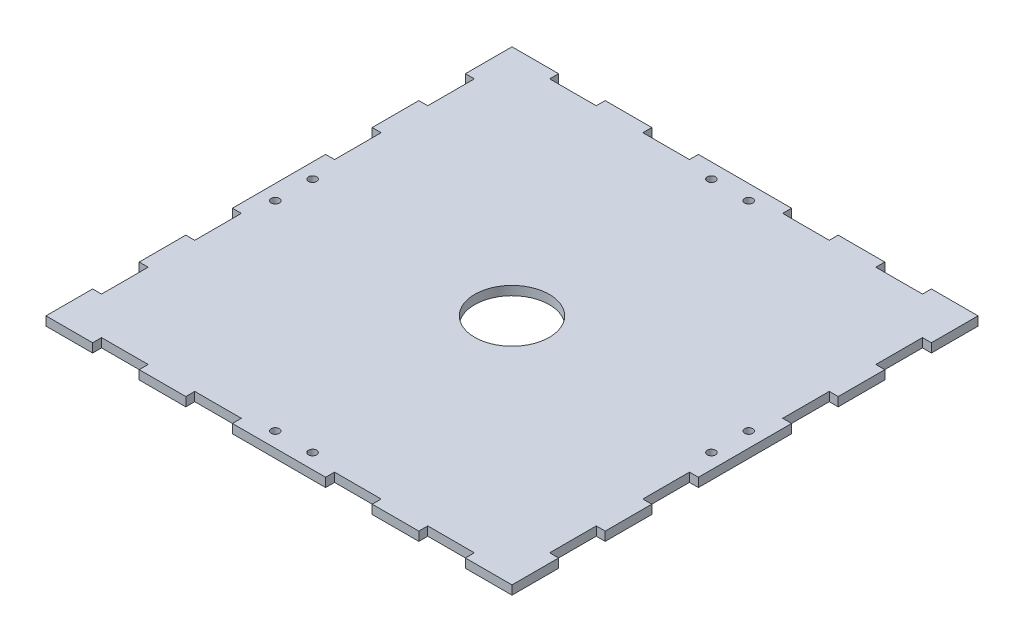
SolidWorks part; units mm, degrees
material "Acrylic (Medium-high impact)"
ref_plane "Front Plane" through (0, 0, 0) normal (0, 0, 1) x (1, 0, 0)
ref_plane "Top Plane" through (0, 0, 0) normal (0, 1, 0) x (1, 0, 0)
ref_plane "Right Plane" through (0, 0, 0) normal (1, 0, 0) x (0, 0, -1)
sketch "Sketch1" plane through (0, 0, 0) normal (0, 1, 0) x (1, 0, 0)
  line L0 (0, 79.375) -> (158.75, 79.375) construction
  line L1 (0, 0) -> (15.875, 0)
  line L2 (0, 0) -> (0, 15.875)
  line L3 (31.75, 158.75) -> (47.625, 158.75)
  line L4 (158.75, 0) -> (158.75, 15.875)
  line L5 (79.375, 158.75) -> (79.375, 0) construction
  line L6 (0, 0) -> (158.75, 158.75) construction
  line L7 (0, 158.75) -> (15.875, 158.75)
  line L8 (15.875, 158.75) -> (15.875, 155.702)
  line L9 (47.625, 158.75) -> (47.625, 155.702)
  line L10 (47.625, 155.702) -> (63.5, 155.702)
  line L11 (63.5, 155.702) -> (63.5, 158.75)
  line L12 (63.5, 158.75) -> (95.25, 158.75)
  line L13 (15.875, 155.702) -> (31.75, 155.702)
  line L14 (31.75, 155.702) -> (31.75, 158.75)
  line L15 (127, 155.702) -> (127, 158.75)
  line L16 (142.875, 155.702) -> (127, 155.702)
  line L17 (95.25, 155.702) -> (95.25, 158.75)
  line L18 (111.125, 155.702) -> (95.25, 155.702)
  line L19 (111.125, 158.75) -> (111.125, 155.702)
  line L20 (142.875, 158.75) -> (142.875, 155.702)
  line L21 (111.125, 158.75) -> (127, 158.75)
  line L22 (142.875, 158.75) -> (158.75, 158.75)
  line L23 (31.75, 3.048) -> (31.75, 0)
  line L24 (15.875, 3.048) -> (31.75, 3.048)
  line L25 (63.5, 3.048) -> (63.5, 0)
  line L26 (47.625, 3.048) -> (63.5, 3.048)
  line L27 (47.625, 0) -> (47.625, 3.048)
  line L28 (15.875, 0) -> (15.875, 3.048)
  line L29 (142.875, 0) -> (142.875, 3.048)
  line L30 (111.125, 0) -> (111.125, 3.048)
  line L31 (111.125, 3.048) -> (95.25, 3.048)
  line L32 (95.25, 3.048) -> (95.25, 0)
  line L33 (142.875, 3.048) -> (127, 3.048)
  line L34 (127, 3.048) -> (127, 0)
  line L35 (63.5, 0) -> (95.25, 0)
  line L36 (31.75, 0) -> (47.625, 0)
  line L37 (111.125, 0) -> (127, 0)
  line L38 (142.875, 0) -> (158.75, 0)
  line L39 (155.702, 31.75) -> (158.75, 31.75)
  line L40 (155.702, 15.875) -> (155.702, 31.75)
  line L41 (155.702, 63.5) -> (158.75, 63.5)
  line L42 (155.702, 47.625) -> (155.702, 63.5)
  line L43 (158.75, 47.625) -> (155.702, 47.625)
  line L44 (158.75, 15.875) -> (155.702, 15.875)
  line L45 (158.75, 142.875) -> (155.702, 142.875)
  line L46 (158.75, 111.125) -> (155.702, 111.125)
  line L47 (155.702, 111.125) -> (155.702, 95.25)
  line L48 (155.702, 95.25) -> (158.75, 95.25)
  line L49 (155.702, 142.875) -> (155.702, 127)
  line L50 (155.702, 127) -> (158.75, 127)
  line L51 (158.75, 142.875) -> (158.75, 158.75)
  line L52 (158.75, 111.125) -> (158.75, 127)
  line L53 (158.75, 63.5) -> (158.75, 95.25)
  line L54 (158.75, 31.75) -> (158.75, 47.625)
  line L55 (3.048, 127) -> (0, 127)
  line L56 (3.048, 142.875) -> (3.048, 127)
  line L57 (3.048, 95.25) -> (0, 95.25)
  line L58 (3.048, 111.125) -> (3.048, 95.25)
  line L59 (0, 111.125) -> (3.048, 111.125)
  line L60 (0, 142.875) -> (3.048, 142.875)
  line L61 (0, 15.875) -> (3.048, 15.875)
  line L62 (0, 47.625) -> (3.048, 47.625)
  line L63 (3.048, 47.625) -> (3.048, 63.5)
  line L64 (3.048, 63.5) -> (0, 63.5)
  line L65 (3.048, 15.875) -> (3.048, 31.75)
  line L66 (3.048, 31.75) -> (0, 31.75)
  line L67 (0, 142.875) -> (0, 158.75)
  line L68 (0, 111.125) -> (0, 127)
  line L69 (0, 63.5) -> (0, 95.25)
  line L70 (0, 31.75) -> (0, 47.625)
  circle A0 centre (79.375, 79.375) radius 12.7
  circle A1 centre (73.025, 153.67) radius 1.397
  circle A2 centre (85.725, 153.67) radius 1.397
  circle A3 centre (153.67, 73.025) radius 1.397
  circle A4 centre (153.67, 85.725) radius 1.397
  circle A5 centre (5.08, 85.725) radius 1.397
  circle A6 centre (5.08, 73.025) radius 1.397
  circle A7 centre (73.025, 5.08) radius 1.397
  circle A8 centre (85.725, 5.08) radius 1.397
  dimension "D3" = 25.4
  dimension "D2" = 2.794
  dimension "D4" = 5.08
  dimension "D5" = 6.35
  dimension "D6" = 3.048
  dimension "D7" = 15.875
  dimension "D8" = 158.75
extrude "Boss-Extrude1" add sketch "Sketch1" along normal blind 3.048
